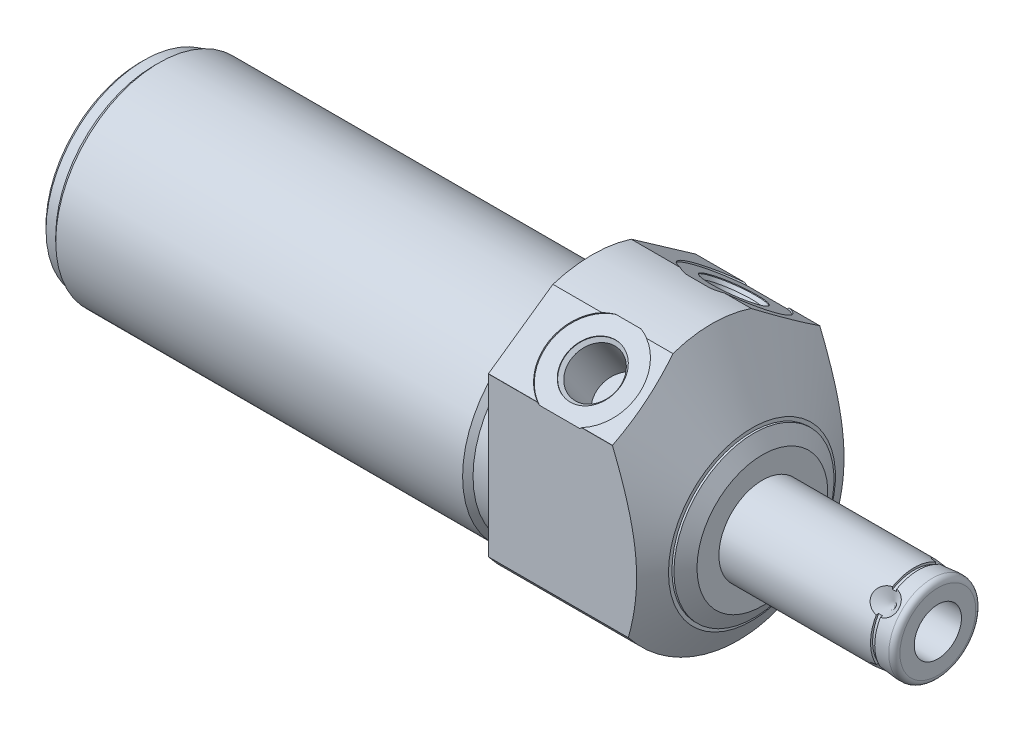
SolidWorks part; units mm, degrees
material "Alloy Steel"
ref_plane "Front Plane" through (0, 0, 0) normal (0, 0, 1) x (1, 0, 0)
ref_plane "Top Plane" through (0, 0, 0) normal (0, 1, 0) x (1, 0, 0)
ref_plane "Right Plane" through (0, 0, 0) normal (1, 0, 0) x (0, 0, -1)
sketch "Sketch1" plane through (0, 0, 0) normal (1, 0, 0) x (0, 0, -1)
  circle A0 centre (0, 0) radius 25.4
  dimension "D1" = 50.8
extrude "Extrude1" add sketch "Sketch1" along normal blind 31.0896 and the other way blind 82.4992
sketch "Sketch2" plane through (0, 0, 0) normal (1, 0, 0) x (0, 0, -1)
  line L0 (-14.6964, -4.191) -> (14.6964, -4.191) construction
  circle A0 centre (0, -4.191) radius 18.8595
  circle A1 centre (0, 0) radius 25.4 construction
  circle A2 centre (0, 0) radius 25.4
  dimension "D1" = 37.719
  dimension "D2" = 4.191
extrude "Cut-Extrude1" cut sketch "Sketch2" against normal up to next
sketch "Sketch4" plane through (31.0896, 0, 0) normal (-1, 0, 0) x (0, 0, 1)
  line L0 (18.923, -14.4553) -> (18.923, 14.4553)
  line L1 (18.9056, 14.4781) -> (7.1389, 22.7172)
  line L2 (-18.923, -14.4553) -> (-18.923, 14.4553)
  line L3 (-18.9056, 14.4781) -> (-7.1389, 22.7172)
  line L4 (0, -20.9029) -> (0, 19.86) construction
  circle A0 centre (0, 0) radius 25.4 construction
  circle A1 centre (0, 0) radius 25.4
  arc A2 (-18.923, -14.4553) -> (18.923, -14.4553) centre (0, 0) ccw
  arc A3 (7.1389, 22.7172) -> (-7.1389, 22.7172) centre (0, 0) ccw
  arc A4 (18.923, 14.4553) -> (18.9056, 14.4781) centre (0, 0) ccw
  arc A6 (-18.9056, 14.4781) -> (-18.923, 14.4553) centre (0, 0) ccw
  dimension "D4" = 23.8125
  dimension "D1" = 37.846
  dimension "D2" = 55
  dimension "D3" = 26.1366
extrude "Cut-Extrude3" cut sketch "Sketch4" along normal up to next
sketch "Sketch6" plane through (0, 0, 0) normal (0, 0, 1) x (1, 0, 0)
  line L0 (16.3314, 33.309) -> (29.1846, 11.0466)
  line L1 (1.9872, -4.191) -> (19.8625, -4.191) construction
  line L2 (-82.4992, -4.191) -> (0, -4.191) construction
  line L4 (31.0896, 7.747) -> (31.0896, 33.309)
  line L5 (31.0896, 33.309) -> (16.3314, 33.309)
  line L7 (29.1846, 11.0466) -> (29.1846, 10.414)
  line L8 (29.1846, 10.414) -> (29.5498, 10.414)
  line L9 (29.5498, 10.414) -> (31.0896, 7.747)
  line L11 (31.0896, -14.4553) -> (31.0896, 14.4553) construction
  dimension "D1" = 23.876
  dimension "D2" = 75
  dimension "D3" = 29.21
  dimension "D4" = 1.905
  dimension "D5" = 30
revolve "Cut-Revolve2" cut sketch "Sketch6" angle 360 about L1
ref_plane "Plane17" through (13.0048, 0, 0) normal (-1, 0, 0) x (0, 0, 1)
sketch "S2D0002" plane through (13.0048, 13.7124, 8.6091) normal (1, 0, 0) x (0, 0.4226, -0.9063)
  line L0 (3.0583, 6.9151) -> (6.2476, 7.4775)
  line L1 (3.0583, 6.9151) -> (3.0804, 6.7901)
  line L2 (3.0804, 6.7901) -> (2.5962, 6.0986)
  line L3 (2.5962, 6.0986) -> (4.1024, -2.4437)
  line L4 (4.1024, -2.4437) -> (-0.25, -3.2112)
  line L5 (-0.25, -3.2112) -> (-1.9261, 6.2942)
  line L6 (1.3861, -12.4899) -> (-0.9428, 0.7176) construction
  line L7 (6.2035, 7.7276) -> (6.2476, 7.4775)
  line L8 (5.1381, 7.5398) -> (-9.0082, 5.0454) construction
  line L9 (6.2035, 7.7276) -> (-1.9261, 6.2942)
  dimension "D1" = 16.51
  dimension "D2" = 0.254
  dimension "D3" = 0.127
  dimension "D4" = 10.033
  dimension "D5" = 45
  dimension "D6" = 8.8392
  dimension "D7" = 9.398
  dimension "D8" = 2.413
revolve "Cut-Revolve3" cut sketch "S2D0002" angle 360 about L6
mirror "Mirror1" about plane through (0, 0, 0) normal (0, 0, 1) of "Cut-Revolve3"
sketch "Sketch10" plane through (0, 0, 0) normal (0, 0, 1) x (1, 0, 0)
  line L0 (0, 14.6685) -> (0, 13.716)
  line L1 (0, 13.716) -> (-3.81, 13.716)
  line L2 (-3.81, 13.716) -> (-4.7625, 14.6685)
  line L3 (-5.094, -4.191) -> (0.2426, -4.191) construction
  line L4 (0, 14.6685) -> (-4.7625, 14.6685)
  line L5 (-82.4992, -4.191) -> (0, -4.191) construction
  line L6 (0, 14.6685) -> (-82.4992, 14.6685) construction
  line L7 (0, 14.4553) -> (0, -14.4553) construction
  dimension "D1" = 35.814
  dimension "D2" = 3.81
  dimension "D3" = 45
revolve "Cut-Revolve6" cut sketch "Sketch10" angle 360 about L3
sketch "Sketch12" plane through (0, 0, 0) normal (0, 0, 1) x (1, 0, 0)
  line L0 (-82.4992, 14.6685) -> (-82.4992, 13.716)
  line L1 (-82.4992, 13.716) -> (-79.9592, 13.716)
  line L2 (-79.9592, 13.716) -> (-79.0067, 14.6685)
  line L3 (-50.9283, -4.191) -> (-48.1063, -4.191) construction
  line L4 (-82.4992, 14.6685) -> (-79.0067, 14.6685)
  line L5 (-82.4992, -4.191) -> (-4.7625, -4.191) construction
  line L6 (-4.7625, 14.6685) -> (-82.4992, 14.6685) construction
  line L7 (-82.4992, 14.6685) -> (-82.4992, -23.0505) construction
  dimension "D1" = 35.814
  dimension "D2" = 2.54
  dimension "D3" = 45
revolve "Cut-Revolve8" cut sketch "Sketch12" angle 360 about L3
chamfer "Chamfer1" distance 0.762 angle 45 1 edges at (-82.4992, -4.191, 17.907)
sketch "Sketch13" plane through (0, 0, 0) normal (0, 0, 1) x (1, 0, 0)
  line L0 (31.0896, -4.191) -> (63.106, -4.191)
  line L1 (63.106, -4.191) -> (63.106, -11.1125)
  line L2 (62.09, -12.1285) -> (31.0896, -12.1285)
  line L3 (31.0896, -12.1285) -> (31.0896, -4.191)
  line L4 (4.7498, -4.191) -> (27.0459, -4.191) construction
  line L5 (-79.0067, -4.191) -> (-4.7625, -4.191) construction
  line L6 (31.0896, -16.129) -> (31.0896, 7.747) construction
  line L7 (0, 14.4553) -> (0, -14.4553) construction
  arc A0 (62.09, -12.1285) -> (63.106, -11.1125) centre (62.09, -11.1125) ccw
  dimension "D2" = 1.016
  dimension "D1" = 63.106
  dimension "D3" = 15.875
revolve "Revolve1" add sketch "Sketch13" angle 360 about L4
ref_plane "Plane18" through (0, -2.0955, -2.0955) normal (0, 0.7071, 0.7071) x (-1, 0, 0)
sketch "S2D0001" plane through (0, 0, 0) normal (0, 0, 1) x (1, 0, 0)
  line L0 (63.106, 0.1143) -> (47.866, 0.1143)
  line L1 (47.866, 0.1143) -> (45.2791, -4.191)
  line L2 (63.106, 0.1143) -> (63.106, -4.191)
  line L3 (63.106, -4.191) -> (45.2791, -4.191)
  line L4 (-2.8067, -4.191) -> (-15.8378, -4.191) construction
  line L5 (62.09, -4.191) -> (31.0896, -4.191) construction
  line L6 (63.106, -11.1125) -> (63.106, 2.7305) construction
  dimension "D1" = 8.6106
  dimension "D2" = 15.24
  dimension "D3" = 59
revolve "Cut-Revolve9" cut sketch "S2D0001" angle 360 about L4
sketch "Sketch16" plane through (0, -7.1545, 2.9635) normal (0, -0.7071, -0.7071) x (1, 0, 0)
  line L0 (59.1436, -12.1285) -> (56.7306, -12.1285)
  line L1 (56.7306, -12.1285) -> (59.1436, -9.7155)
  line L2 (59.1436, -12.1285) -> (59.1436, -9.7155)
  line L3 (59.1436, -3.4788) -> (59.1436, 0.0794) construction
  line L4 (63.106, -11.1125) -> (63.106, 2.7305) construction
  line L5 (31.0896, -12.1285) -> (62.09, -12.1285) construction
  dimension "D1" = 3.9624
  dimension "D2" = 4.826
  dimension "D3" = 45
revolve "Cut-Revolve10" cut sketch "Sketch16" angle 360 about L3
pattern_circular "CirPattern1" count 4 over 360 about axis through (4.7498, -4.191, 0) along (-1, 0, 0) of "Cut-Revolve10"
sketch "Sketch21" plane through (0, 0, 0) normal (0, 0, 1) x (1, 0, 0)
  line L1 (58.7626, 3.7465) -> (59.5246, 3.7465)
  line L2 (58.7626, 3.7465) -> (58.7626, 3.3655)
  line L3 (58.7626, 3.3655) -> (59.5246, 3.3655)
  line L4 (59.5246, 3.7465) -> (59.5246, 3.3655)
  line L5 (59.1436, -0.7782) -> (59.1436, 2.3032) construction
  line L7 (23.8735, -4.191) -> (50.6625, -4.191) construction
  line L10 (63.106, -11.1125) -> (63.106, 2.7305) construction
  line L11 (66.5847, -4.191) -> (53.1006, -4.191) construction
  dimension "D1" = 0.381
  dimension "D2" = 0.762
  dimension "D3" = 3.5814
  dimension "D4" = 7.9375
revolve "Cut-Revolve11" cut sketch "Sketch21" angle 360 about L7
